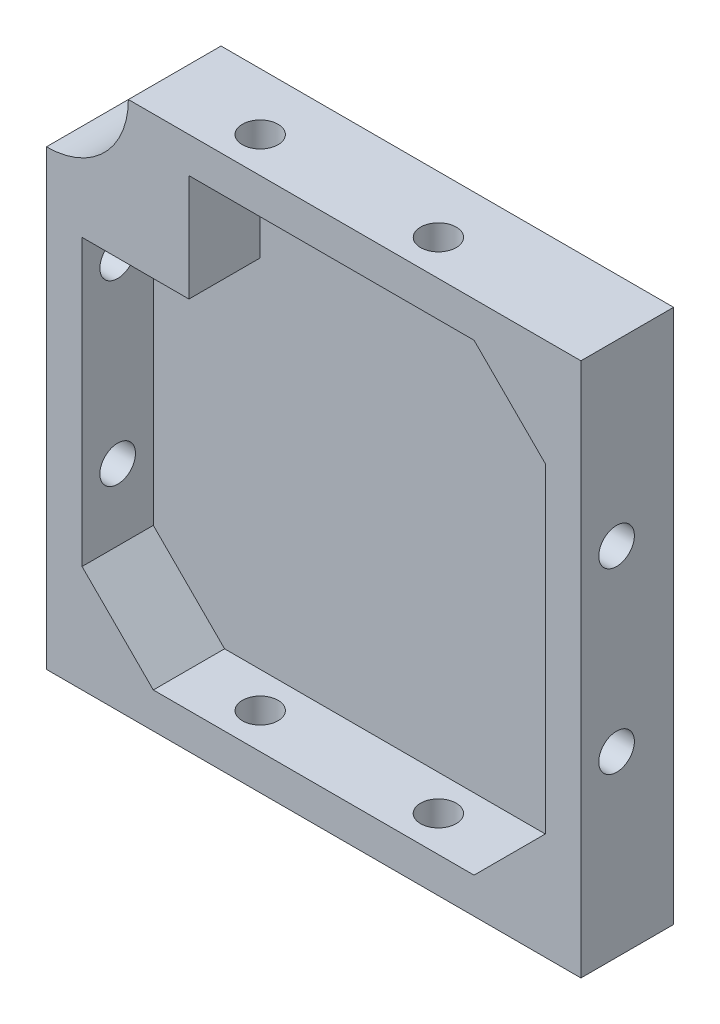
SolidWorks part; units mm, degrees
ref_plane "Plan de face" through (0, 0, 0) normal (0, 0, 1) x (1, 0, 0)
ref_plane "Plan de dessus" through (0, 0, 0) normal (0, 1, 0) x (1, 0, 0)
ref_plane "Plan de droite" through (0, 0, 0) normal (1, 0, 0) x (0, 0, -1)
sketch "Esquisse1" plane through (0, 0, 0) normal (0, 0, 1) x (1, 0, 0)
  line L0 (44.1184, 33.7284) -> (54.1184, 33.7284)
  line L1 (-20.8816, 33.7284) -> (44.1184, 33.7284)
  line L2 (-20.8816, 33.7284) -> (-20.8816, -41.2716)
  line L3 (-20.8816, -41.2716) -> (54.1184, -41.2716)
  line L4 (54.1184, 23.7284) -> (54.1184, -41.2716)
  line L5 (54.1184, 33.7284) -> (54.1184, 23.7284)
  point P6 (54.1184, 33.7284)
  dimension "D1" = 75
  dimension "D2" = 75
extrude "Boss.-Extru.1" add sketch "Esquisse1" along normal blind 13
shell "Coque1" thickness 5
sketch "Esquisse2" plane through (-20.8816, 0, 0) normal (-1, 0, 0) x (0, 0, 1)
  line L0 (13, 33.7284) -> (13, -41.2716) construction
  line L1 (13, 33.7284) -> (0, 33.7284) construction
  line L2 (13, -41.2716) -> (0, -41.2716) construction
  circle A0 centre (8, 8.7284) radius 2.5
  circle A1 centre (8, -16.2716) radius 2.5
  dimension "D1" = 5
  dimension "D2" = 5
  dimension "D3" = 5
  dimension "D4" = 5
  dimension "D5" = 25
  dimension "D6" = 25
extrude "Enlèv. mat.-Extru.1" cut sketch "Esquisse2" against normal up to surface (75 mm away) contours A1 | A0 up to face at (54.1184, -3.7716, 6.5)
sketch "Esquisse3" plane through (0, -41.2716, 0) normal (0, -1, 0) x (1, 0, 0)
  line L0 (-20.8816, 13) -> (54.1184, 13) construction
  line L2 (54.1184, 13) -> (54.1184, 0) construction
  line L3 (-20.8816, 13) -> (-20.8816, 0) construction
  circle A0 centre (4.1184, 8) radius 2.5
  circle A1 centre (29.1184, 8) radius 2.5
  dimension "D1" = 5
  dimension "D2" = 5
  dimension "D3" = 5
  dimension "D4" = 5
  dimension "D5" = 25
  dimension "D6" = 25
extrude "Enlèv. mat.-Extru.2" cut sketch "Esquisse3" against normal up to surface (75 mm away) up to face at (16.6184, 33.7284, 6.5)
sketch "Esquisse4" plane through (0, 0, 3) normal (0, 0, 1) x (1, 0, 0)
  line L0 (-15.8816, -26.2716) -> (-5.8816, -36.2716)
  line L1 (49.1184, 28.7284) -> (-15.8816, 28.7284) construction
  line L3 (-15.8816, 28.7284) -> (-15.8816, -36.2716) construction
  line L4 (-5.8816, -36.2716) -> (-15.8816, -36.2716)
  line L5 (49.1184, 28.7284) -> (49.1184, 18.7284)
  line L6 (49.1184, -36.2716) -> (49.1184, 28.7284) construction
  line L7 (49.1184, 18.7284) -> (39.1184, 28.7284)
  line L8 (39.1184, 28.7284) -> (49.1184, 28.7284)
  line L9 (49.1184, 28.7284) -> (-15.8816, 28.7284) construction
  line L10 (49.1184, -36.2716) -> (49.1184, -26.2716)
  line L11 (49.1184, -26.2716) -> (39.1184, -36.2716)
  line L12 (-15.8816, -36.2716) -> (49.1184, -36.2716) construction
  line L13 (39.1184, -36.2716) -> (49.1184, -36.2716)
  line L14 (-15.8816, -36.2716) -> (-15.8816, -26.2716)
  line L16 (-15.8816, 28.7284) -> (-0.8816, 28.7284)
  line L17 (-15.8816, 28.7284) -> (-15.8816, 13.7284)
  line L18 (-15.8816, 13.7284) -> (-0.8816, 13.7284)
  line L19 (-0.8816, 28.7284) -> (-0.8816, 13.7284)
  dimension "D1" = 10
  dimension "D2" = 10
  dimension "D3" = 10
  dimension "D4" = 10
  dimension "D5" = 10
  dimension "D6" = 10
  dimension "D7" = 15
  dimension "D8" = 15
extrude "Boss.-Extru.2" add sketch "Esquisse4" along normal up to surface (10 mm away) up to face at (16.6184, -3.7716, 13)
sketch "Esquisse5" plane through (0, 0, 13) normal (0, 0, 1) x (1, 0, 0)
  line L0 (54.1184, 33.7284) -> (-20.8816, 33.7284) construction
  line L1 (-20.8816, 33.7284) -> (-20.8816, -41.2716) construction
  circle A0 centre (-20.8816, 33.7284) radius 11.5
  dimension "D1" = 23
extrude "Enlèv. mat.-Extru.3" cut sketch "Esquisse5" against normal up to surface (13 mm away) up to face at (16.6184, -3.7716, 0)
